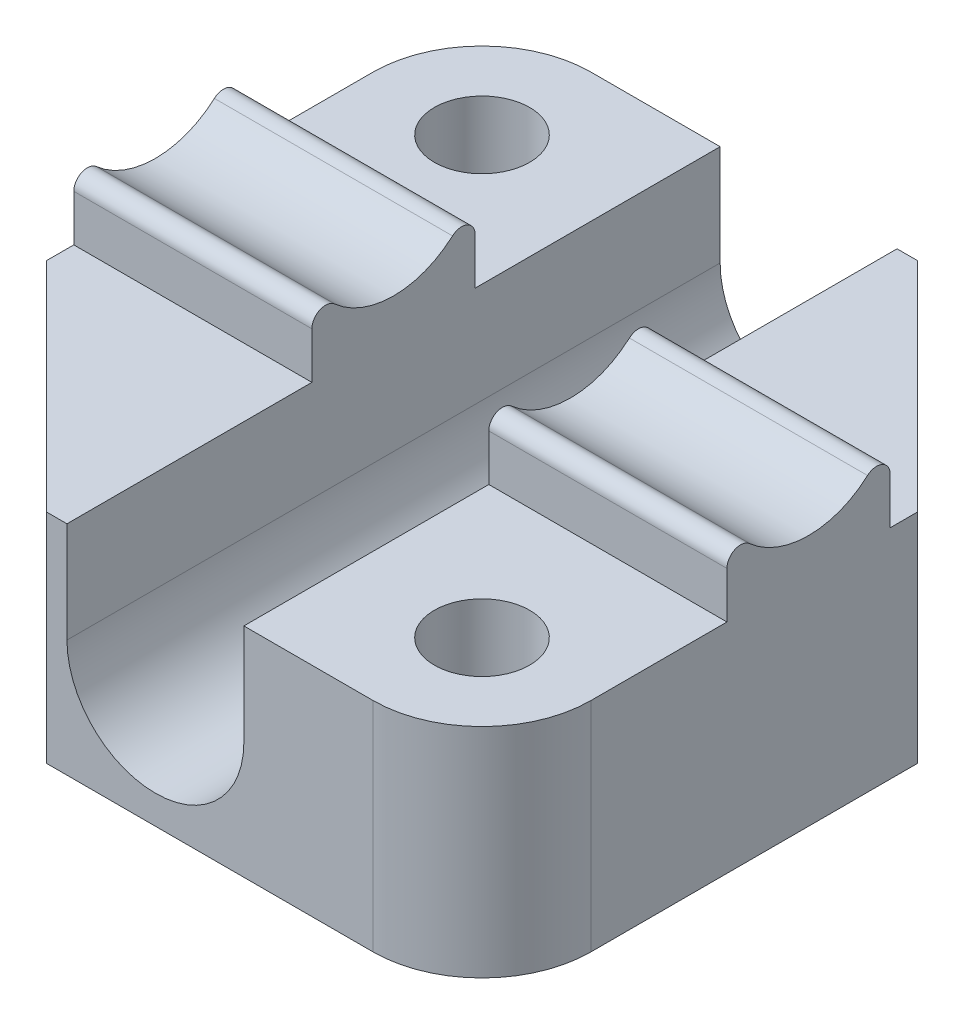
SolidWorks part; units mm, degrees
ref_plane "前视基准面" through (0, 0, 0) normal (0, 0, 1) x (1, 0, 0)
ref_plane "上视基准面" through (0, 0, 0) normal (0, 1, 0) x (1, 0, 0)
ref_plane "右视基准面" through (0, 0, 0) normal (1, 0, 0) x (0, 0, -1)
sketch "草图1" plane through (0, 0, 0) normal (0, 1, 0) x (1, 0, 0)
  line L1 (-12, -12) -> (12, -12)
  line L2 (-12, -12) -> (-12, 12)
  line L3 (-12, 12) -> (12, 12)
  line L4 (12, -12) -> (12, 12)
  line L5 (-12, -12) -> (12, 12) construction
  line L6 (-12, 12) -> (12, -12) construction
  point P0 (0, 0)
  dimension "D1" = 24
extrude "凸台-拉伸1" add sketch "草图1" along normal blind 8
sketch "草图2" plane through (0, 0, 12) normal (0, 0, 1) x (1, 0, 0)
  line L0 (0, 0) -> (0, 11.7448) construction
  line L2 (-12, 8) -> (12, 8) construction
  line L3 (-3.25, 4.3) -> (3.25, 4.3)
  line L4 (-3.25, 4.3) -> (-3.25, 8)
  line L5 (-3.25, 8) -> (3.25, 8)
  line L6 (3.25, 4.3) -> (3.25, 8)
  circle A0 centre (0, 4.3) radius 3.25
  line M5 (12, 8) -> (-12, 8)
  dimension "D1" = 6.5
  dimension "D2" = 3.7
extrude "切除-拉伸1" cut sketch "草图2" against normal through all and the other way through all contours A0 L0 L5 L4 | L0 A0 L6 M5 | L0 L3 A0 | L3 L0 A0 | A0 L0 L3 | L0 A0 L3
sketch "草图4" plane through (12, 0, 0) normal (1, 0, 0) x (0, 0, -1)
  line L0 (0, 0) -> (0, 12.1904) construction
  line L1 (-3, 11.25) -> (3, 11.25) construction
  line L2 (-12, 8) -> (12, 8) construction
  line L3 (-3, 8) -> (3, 8)
  line L4 (-3, 8) -> (-3, 11.25)
  line L6 (3, 8) -> (3, 11.25)
  arc A1 (-3, 11.25) -> (3, 11.25) centre (0, 12.5) ccw
  dimension "D2" = 6
  dimension "D1" = 3.25
  dimension "D3" = 4.5
extrude "凸台-拉伸2" add sketch "草图4" against normal blind 8.75 contours L6 A1 L4 L3
mirror "镜向2" about plane through (0, 0, 0) normal (1, 0, 0) of "凸台-拉伸2"
sketch "草图5" plane through (0, 8, 0) normal (0, 1, 0) x (1, 0, 0)
  line L0 (-12, 12) -> (12, -12) construction
  line L1 (-12, 12) -> (-12, 3) construction
  line L2 (0, 0) -> (12, 12) construction
  circle A0 centre (-8, 8) radius 1.75
  circle A1 centre (8, -8) radius 1.75
  dimension "D1" = 3.5
  dimension "D2" = 4
extrude "切除-拉伸3" cut sketch "草图5" against normal through all
chamfer "倒角1" distance 8 angle 45 2 edges at (12, 4, -12) (-12, 4, 12)
fillet "圆角1" radius 4 2 edges at (12, 4, 12) (-12, 4, -12)
fillet "圆角2" radius 0.5 4 edges at (7.625, 11.25, -3) (-7.625, 11.25, -3) (-7.625, 11.25, 3) (7.625, 11.25, 3)
sketch "草图9" plane through (0, 0, 0) normal (0, -1, 0) x (1, 0, 0)
  circle A0 centre (0, 0) radius 2
  dimension "D1" = 4
extrude "切除-拉伸4" cut sketch "草图9" against normal through all
chamfer "倒角3" distance 0.5 angle 45 2 edges at (8, 0, 6.25) (-8, 0, -6.25)
